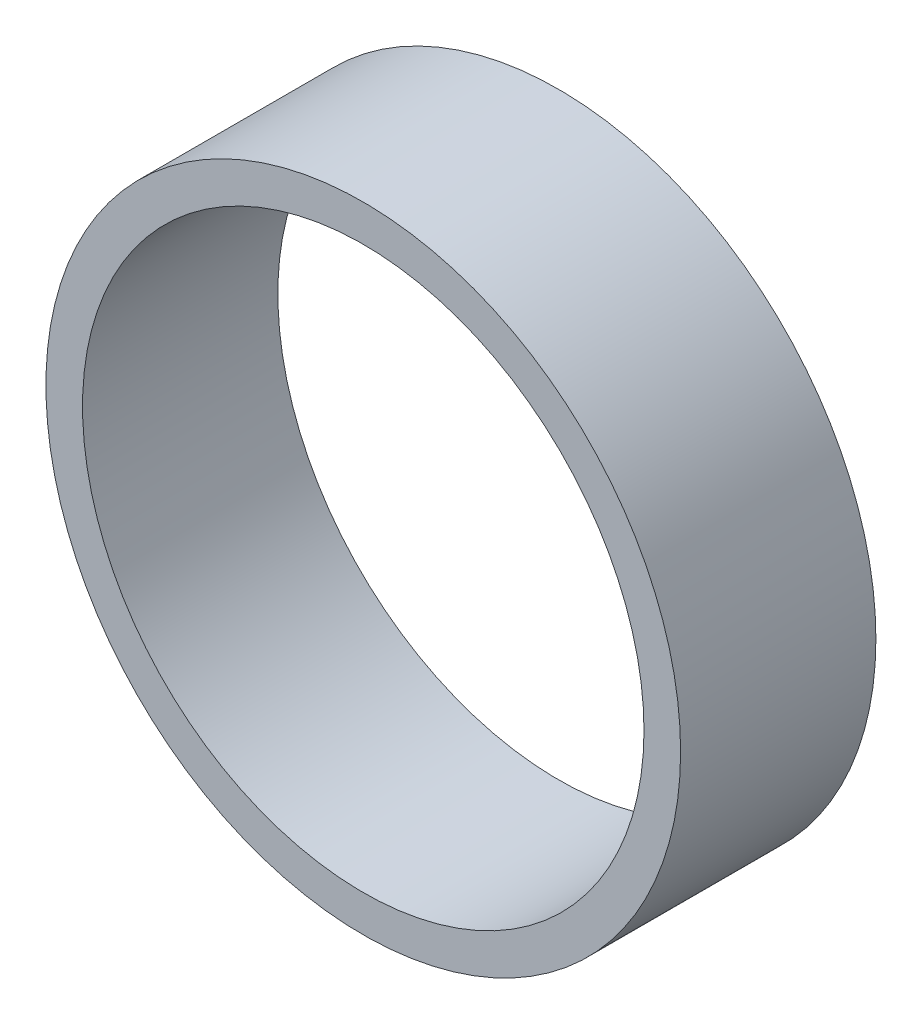
SolidWorks part; units mm, degrees
ref_plane "Спереди" through (0, 0, 0) normal (0, 0, 1) x (1, 0, 0)
ref_plane "Сверху" through (0, 0, 0) normal (0, 1, 0) x (1, 0, 0)
ref_plane "Справа" through (0, 0, 0) normal (1, 0, 0) x (0, 0, -1)
sketch "Эскиз1" plane through (0, 0, 0) normal (0, 0, 1) x (1, 0, 0)
  circle A0 centre (0, 0) radius 13
  circle A1 centre (0, 0) radius 7
  circle A2 centre (0, 0) radius 8.5
  circle A3 centre (0, 0) radius 11.5
  circle A4 centre (0, 10) radius 2.25
  dimension "D1" = 23
  dimension "D2" = 26
  dimension "D3" = 17
  dimension "D4" = 14
  dimension "D5" = 10
sketch "Эскиз2" plane through (0, 0, 0) normal (0, 0, 1) x (1, 0, 0)
  circle A0 centre (0, 0) radius 13
  circle A1 centre (0, 0) radius 7
  circle A2 centre (0, 0) radius 8.5
  circle A3 centre (0, 0) radius 11.5
  circle A4 centre (0, 10) radius 2.25
  dimension "D1" = 23
  dimension "D2" = 26
  dimension "D3" = 17
  dimension "D4" = 14
  dimension "D5" = 10
sketch "Эскиз3" plane through (0, 0, 0) normal (0, 0, 1) x (1, 0, 0)
  circle A0 centre (0, 0) radius 13
  circle A1 centre (0, 0) radius 7
  circle A2 centre (0, 0) radius 8.5
  circle A3 centre (0, 0) radius 11.5
  circle A4 centre (0, 10) radius 2.25
  dimension "D1" = 23
  dimension "D2" = 26
  dimension "D3" = 17
  dimension "D4" = 14
  dimension "D5" = 10
extrude "Бобышка-Вытянуть1" add sketch "Эскиз1" along normal blind 8 contours A3 | A0
